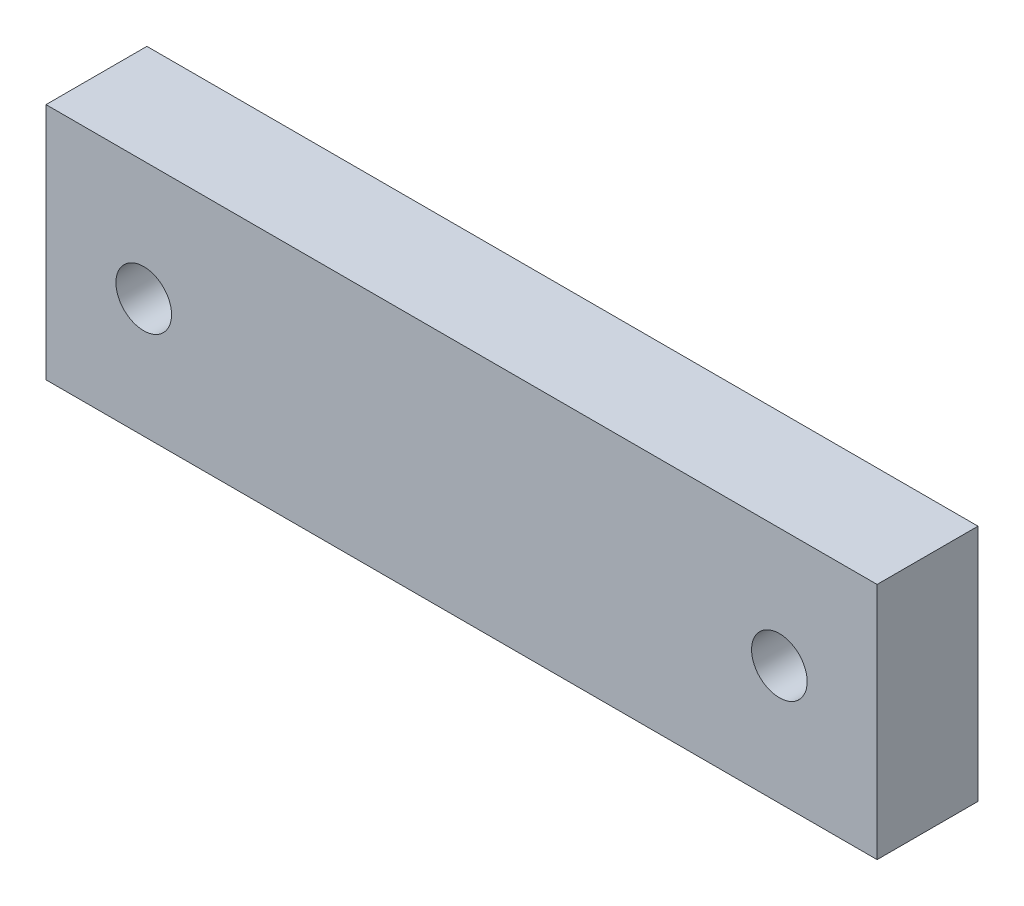
SolidWorks part; units mm, degrees
ref_plane "Front Plane" through (0, 0, 0) normal (0, 0, 1) x (1, 0, 0)
ref_plane "Top Plane" through (0, 0, 0) normal (0, 1, 0) x (1, 0, 0)
ref_plane "Right Plane" through (0, 0, 0) normal (1, 0, 0) x (0, 0, -1)
sketch "Sketch1" plane through (0, 0, 0) normal (0, 0, 1) x (1, 0, 0)
  line L0 (6.15, 7.5) -> (46.15, 7.5) construction
  line L1 (0, 0) -> (52.3, 0)
  line L2 (0, 0) -> (0, 15)
  line L3 (0, 15) -> (52.3, 15)
  line L4 (52.3, 0) -> (52.3, 15)
  circle A0 centre (6.15, 7.5) radius 1.75
  circle A1 centre (46.15, 7.5) radius 1.75
  point P9 (52.3, 7.5)
  point P10 (26.15, 7.5)
  point P11 (26.15, 15)
  dimension "D4" = 3.5
  dimension "D1" = 40
  dimension "D2" = 15
  dimension "D3" = 52.3
extrude "Boss-Extrude1" add sketch "Sketch1" along normal blind 6.35
